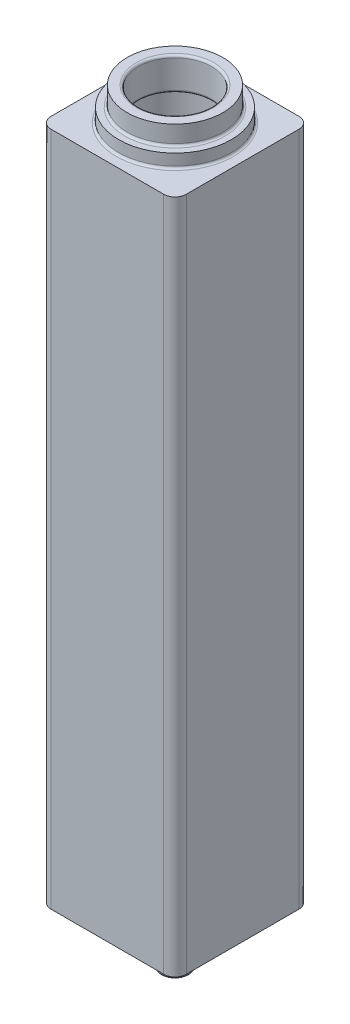
SolidWorks part; units mm, degrees
ref_plane "Plan de face" through (0, 0, 0) normal (0, 0, 1) x (1, 0, 0)
ref_plane "Plan de dessus" through (0, 0, 0) normal (0, 1, 0) x (1, 0, 0)
ref_plane "Plan de droite" through (0, 0, 0) normal (1, 0, 0) x (0, 0, -1)
sketch "Esquisse1" plane through (0, 0, 0) normal (0, 1, 0) x (1, 0, 0)
  line L1 (-60, -60) -> (60, -60)
  line L2 (-60, -60) -> (-60, 60)
  line L3 (-60, 60) -> (60, 60)
  line L4 (60, -60) -> (60, 60)
  line L5 (-60, -60) -> (60, 60) construction
  line L6 (-60, 60) -> (60, -60) construction
  point P0 (0, 0)
  dimension "D1" = 120
  dimension "D2" = 120
extrude "Boss.-Extru.1" add sketch "Esquisse1" along normal blind 600
fillet "Congé1" radius 10 1 edges at (60, 300, 60)
fillet "Congé2" radius 10 1 edges at (60, 300, -60)
fillet "Congé3" radius 10 1 edges at (-60, 300, -60)
fillet "Congé4" radius 10 1 edges at (-60, 300, 60)
sketch "Esquisse2" plane through (0, 600, 0) normal (0, 1, 0) x (1, 0, 0)
  circle A0 centre (0, 0) radius 42.5
  dimension "D1" = 85
extrude "Boss.-Extru.2" add sketch "Esquisse2" along normal blind 29
sketch "Esquisse4" plane through (0, 600, 0) normal (0, 1, 0) x (1, 0, 0)
  circle A0 centre (0, 0) radius 50
  dimension "D1" = 100
extrude "Boss.-Extru.3" add sketch "Esquisse4" along normal blind 12
sketch "Esquisse8" plane through (0, 0, 0) normal (0, -1, 0) x (1, 0, 0)
  circle A0 centre (0, 0) radius 45
  dimension "D1" = 90
extrude "Boss.-Extru.4" add sketch "Esquisse8" along normal blind 12
sketch "Esquisse9" plane through (0, 0, 0) normal (0, -1, 0) x (1, 0, 0)
  circle A0 centre (0, 0) radius 12.5
  dimension "D1" = 25
extrude "Boss.-Extru.5" add sketch "Esquisse9" along normal blind 50
sketch "Esquisse5" plane through (0, 600, 0) normal (0, 1, 0) x (1, 0, 0)
  circle A0 centre (0, 0) radius 35
  dimension "D1" = 70
extrude "Enlèv. mat.-Extru.1" cut sketch "Esquisse5" against normal blind 590
fillet "Congé5" radius 2 2 edges at (0, -12, -45) (0, -12, -12.5)
fillet "Congé6" radius 2 1 edges at (0, -50, -12.5)
fillet "Congé7" radius 2 1 edges at (0, 600, -50)
sketch "Esquisse11" plane through (0, 629, 0) normal (0, 1, 0) x (1, 0, 0)
  circle A0 centre (0, 0) radius 32.5
extrude "Enlèv. mat.-Extru.3" cut sketch "Esquisse11" against normal blind 29
fillet "Congé9" radius 2 1 edges at (0, 600, 32.5)
fillet "Congé11" radius 2 1 edges at (0, 612, 42.5)
fillet "Congé12" radius 2 1 edges at (0, 629, 32.5)
